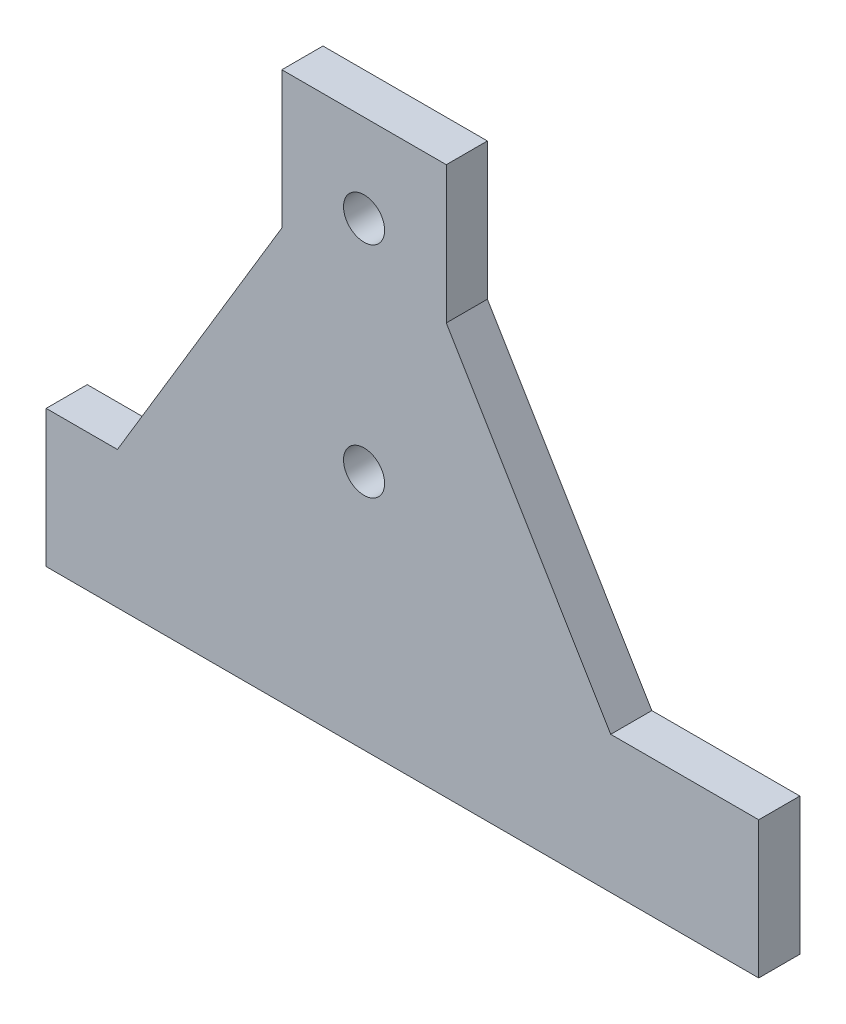
SolidWorks part; units mm, degrees
ref_plane "Plan de face" through (0, 0, 0) normal (0, 0, 1) x (1, 0, 0)
ref_plane "Plan de dessus" through (0, 0, 0) normal (0, 1, 0) x (1, 0, 0)
ref_plane "Plan de droite" through (0, 0, 0) normal (1, 0, 0) x (0, 0, -1)
sketch "Esquisse1" plane through (0, 0, 0) normal (0, 0, 1) x (1, 0, 0)
  line L0 (-130, 0) -> (-130, 50)
  line L1 (-130, 50) -> (-104, 50)
  line L2 (-104, 50) -> (-44, 150)
  line L3 (-44, 150) -> (-44, 200)
  line L4 (-44, 200) -> (16, 200)
  line L5 (16, 200) -> (16, 150)
  line L6 (16, 150) -> (76, 50)
  line L7 (76, 50) -> (130, 50)
  line L8 (130, 50) -> (130, 0)
  line L9 (130, 0) -> (-130, 0)
  circle A0 centre (-14, 168) radius 7.5
  circle A1 centre (-14, 88) radius 7.5
  point P2 (0, 0)
  dimension "D9" = 15
  dimension "D11" = 15
  dimension "D12" = 80
  dimension "D1" = 60
  dimension "D2" = 50
  dimension "D3" = 26
  dimension "D4" = 100
  dimension "D5" = 260
  dimension "D6" = 60
  dimension "D7" = 60
  dimension "D8" = 150
  dimension "D10" = 32
extrude "Boss.-Extru.1" add sketch "Esquisse1" along normal blind 15
